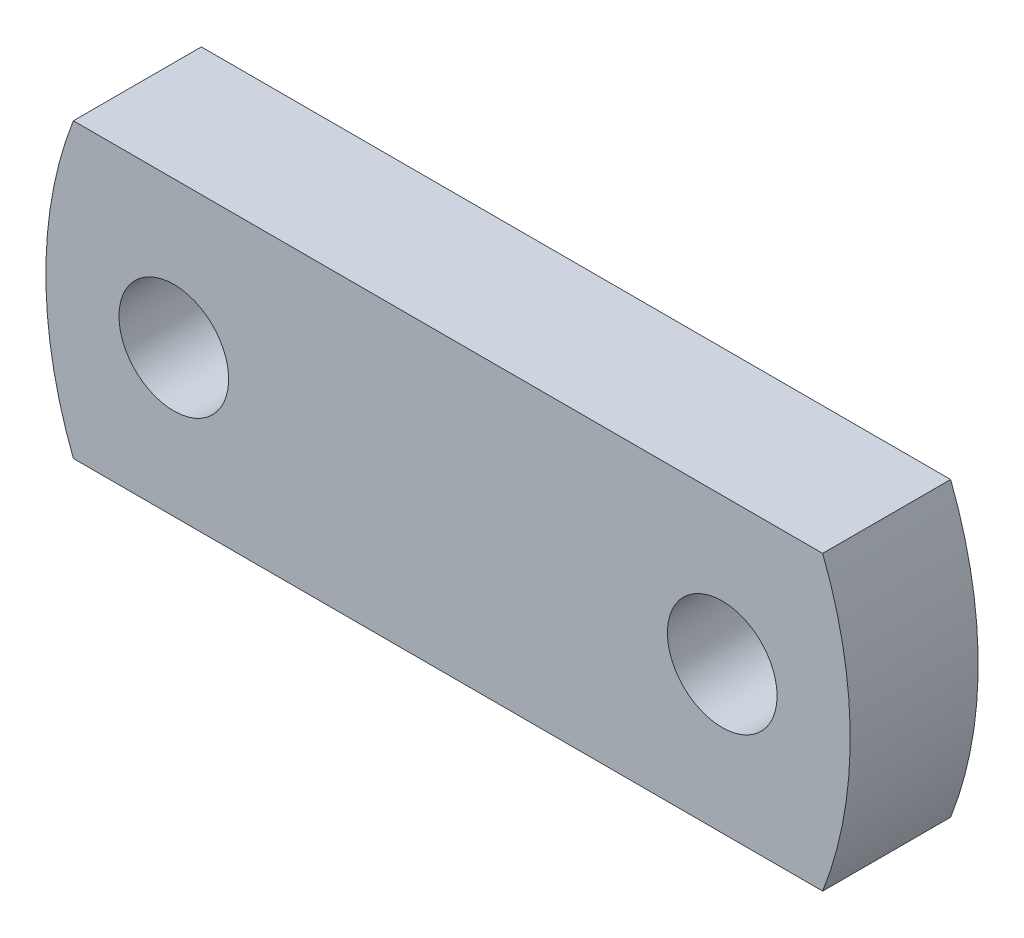
SolidWorks part; units mm, degrees
ref_plane "Front Plane" through (0, 0, 0) normal (0, 0, 1) x (1, 0, 0)
ref_plane "Top Plane" through (0, 0, 0) normal (0, 1, 0) x (1, 0, 0)
ref_plane "Right Plane" through (0, 0, 0) normal (1, 0, 0) x (0, 0, -1)
sketch "Sketch1" plane through (0, 0, 0) normal (0, 0, 1) x (1, 0, 0)
  line L0 (0, 0) -> (75, 0) construction
  line L1 (0, 0) -> (0, 40.708) construction
  line L2 (-102.4695, 40) -> (102.4695, 40)
  line L3 (-102.4695, -40) -> (102.4695, -40)
  arc A0 (-102.4695, 40) -> (-102.4695, -40) centre (0, 0) ccw
  circle A1 centre (75, 0) radius 15
  circle A2 centre (-75, 0) radius 15
  arc A3 (102.4695, -40) -> (102.4695, 40) centre (0, 0) ccw
  dimension "D1" = 220
  dimension "D3" = 30
  dimension "D2" = 75
  dimension "D4" = 40
extrude "Boss-Extrude1" add sketch "Sketch1" along normal blind 35
